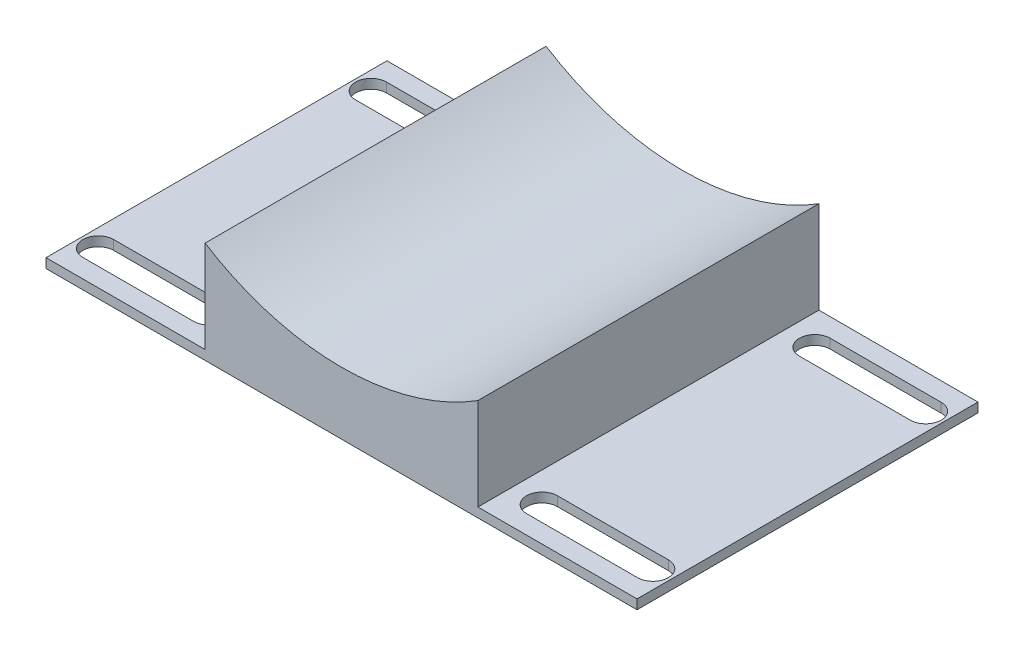
SolidWorks part; units mm, degrees
ref_plane "Front Plane" through (0, 0, 0) normal (0, 0, 1) x (1, 0, 0)
ref_plane "Top Plane" through (0, 0, 0) normal (0, 1, 0) x (1, 0, 0)
ref_plane "Right Plane" through (0, 0, 0) normal (1, 0, 0) x (0, 0, -1)
sketch "Sketch2" plane through (0, 0, 0) normal (0, 0, 1) x (1, 0, 0)
  line L0 (38.1, 1.3208) -> (82.55, 1.3208)
  line L1 (-82.55, 1.3208) -> (-38.1, 1.3208)
  line L2 (-82.55, 1.3208) -> (-82.55, -1.3208)
  line L3 (-82.55, -1.3208) -> (82.55, -1.3208)
  line L4 (82.55, 1.3208) -> (82.55, -1.3208)
  line L5 (-82.55, 1.3208) -> (82.55, -1.3208) construction
  line L6 (-82.55, -1.3208) -> (82.55, 1.3208) construction
  line L8 (-38.1, 27.0748) -> (-38.1, 1.3208)
  line L10 (38.1, 27.0748) -> (38.1, 1.3208)
  arc A0 (-38.1, 27.0748) -> (38.1, 27.0748) centre (0, 87.5792) ccw
  point P0 (0, 0)
  dimension "D3" = 143.002
  dimension "D1" = 2.6416
  dimension "D2" = 165.1
  dimension "D4" = 88.9
  dimension "D5" = 0
  dimension "D6" = 38.1
  dimension "D7" = 38.1
extrude "Boss-Extrude1" add sketch "Sketch2" along normal blind 95.25
sketch "Sketch3" plane through (0, 1.3208, 0) normal (0, 1, 0) x (1, 0, 0)
  line L0 (-77.47, -9.525) -> (-46.482, -9.525) construction
  line L1 (-77.47, -5.207) -> (-46.482, -5.207)
  line L2 (-77.47, -13.843) -> (-46.482, -13.843)
  line L3 (-38.1, 0) -> (-82.55, 0) construction
  line L4 (0, 0) -> (0, -112.7415) construction
  line L5 (-77.47, -85.725) -> (-46.482, -85.725) construction
  line L6 (-77.47, -81.407) -> (-46.482, -81.407)
  line L7 (-77.47, -90.043) -> (-46.482, -90.043)
  arc A0 (-77.47, -5.207) -> (-77.47, -13.843) centre (-77.47, -9.525) ccw
  arc A1 (-46.482, -13.843) -> (-46.482, -5.207) centre (-46.482, -9.525) ccw
  arc A2 (-77.47, -81.407) -> (-77.47, -90.043) centre (-77.47, -85.725) ccw
  arc A3 (-46.482, -90.043) -> (-46.482, -81.407) centre (-46.482, -85.725) ccw
  point P2 (-61.976, -9.525)
  point P14 (-61.976, -85.725)
  dimension "D1" = 61.976
  dimension "D2" = 30.988
  dimension "D3" = 8.636
  dimension "D4" = 9.525
  dimension "D5" = 8.636
  dimension "D6" = 76.2
  dimension "D7" = 30.988
extrude "Cut-Extrude1" cut sketch "Sketch3" against normal blind 95.25
mirror "Mirror2" about plane through (0, 0, 0) normal (1, 0, 0) of "Cut-Extrude1"
